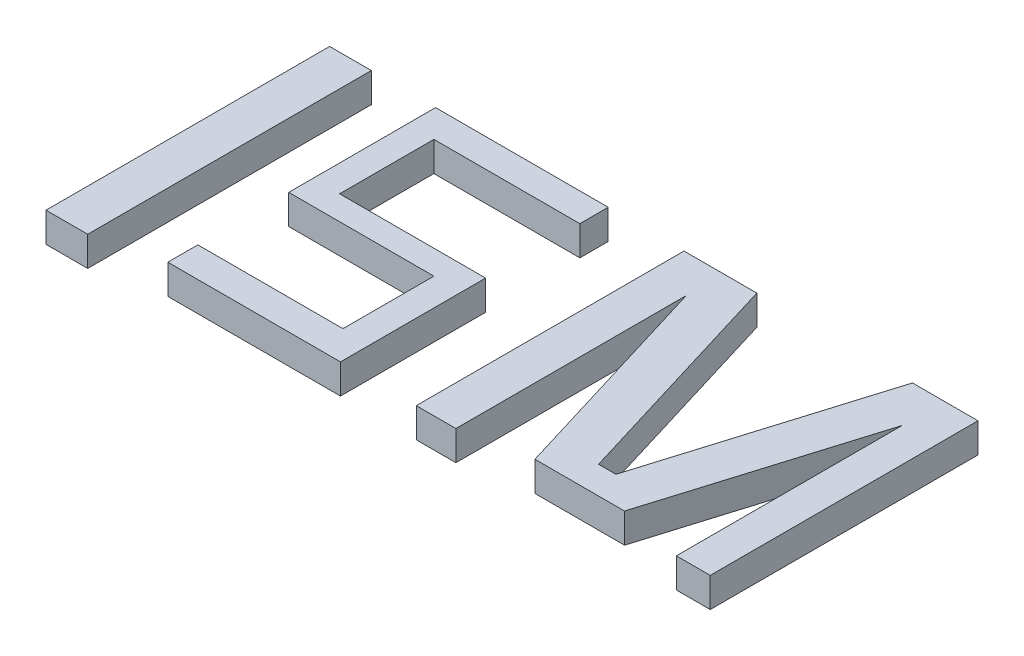
SolidWorks part; units mm, degrees
ref_plane "Front Plane" through (0, 0, 0) normal (0, 0, 1) x (1, 0, 0)
ref_plane "Top Plane" through (0, 0, 0) normal (0, 1, 0) x (1, 0, 0)
ref_plane "Right Plane" through (0, 0, 0) normal (1, 0, 0) x (0, 0, -1)
sketch "Sketch1" plane through (0, 0, 0) normal (0, 1, 0) x (1, 0, 0)
  line L1 (-65.7421, 51.9461) -> (-51.6646, 51.9461)
  line L2 (-65.7421, 51.9461) -> (-65.7421, -43.7811)
  line L3 (-65.7421, -43.7811) -> (-51.6646, -43.7811)
  line L4 (-51.6646, 51.9461) -> (-51.6646, -43.7811)
  line L5 (53.8812, -38.4317) -> (53.8812, 51.9461)
  line L6 (28.2958, 51.9461) -> (-29.9851, 51.9461)
  line L7 (-29.9851, 51.9461) -> (-29.9851, 2.3932)
  line L8 (-29.9851, 2.3932) -> (19.0047, 2.3932)
  line L9 (19.0047, 2.3932) -> (19.0047, -28.2958)
  line L10 (19.0047, -28.2958) -> (-29.9851, -28.2958)
  line L11 (-29.9851, -28.2958) -> (-29.9851, -38.4317)
  line L12 (-29.9851, -38.4317) -> (28.2958, -38.4317)
  line L13 (28.2958, -38.4317) -> (28.2958, 10.5582)
  line L14 (28.2958, 10.5582) -> (-20.9755, 10.5582)
  line L15 (-20.9755, 10.5582) -> (-20.9755, 42.3734)
  line L16 (-20.9755, 42.3734) -> (28.2958, 42.3734)
  line L17 (28.2958, 42.3734) -> (28.2958, 51.9461)
  line L18 (53.8812, 51.9461) -> (78.4506, 51.9461)
  line L19 (78.4506, 51.9461) -> (101.7886, -24.8077)
  line L20 (101.7886, -24.8077) -> (107.6362, -24.8077)
  line L22 (89.5775, -34.0822) -> (67.256, 39.3285)
  line L23 (67.256, 39.3285) -> (67.256, -38.4317)
  line L24 (67.256, -38.4317) -> (53.8812, -38.4317)
  line L25 (89.5775, -34.0822) -> (119.824, -34.0822)
  line L26 (130.9742, 51.9461) -> (107.6362, -24.8077)
  line L27 (141.6653, -38.4317) -> (153.0967, -38.4317)
  line L28 (141.6653, 37.7495) -> (141.6653, -38.4317)
  line L29 (119.824, -34.0822) -> (141.6653, 37.7495)
  line L30 (153.0967, 51.9461) -> (130.9742, 51.9461)
  line L31 (153.0967, -38.4317) -> (153.0967, 51.9461)
  point P8 (97.4439, 5.7718)
  point P10 (0, 5.7718)
extrude "Boss-Extrude1" add sketch "Sketch1" along normal blind 10
